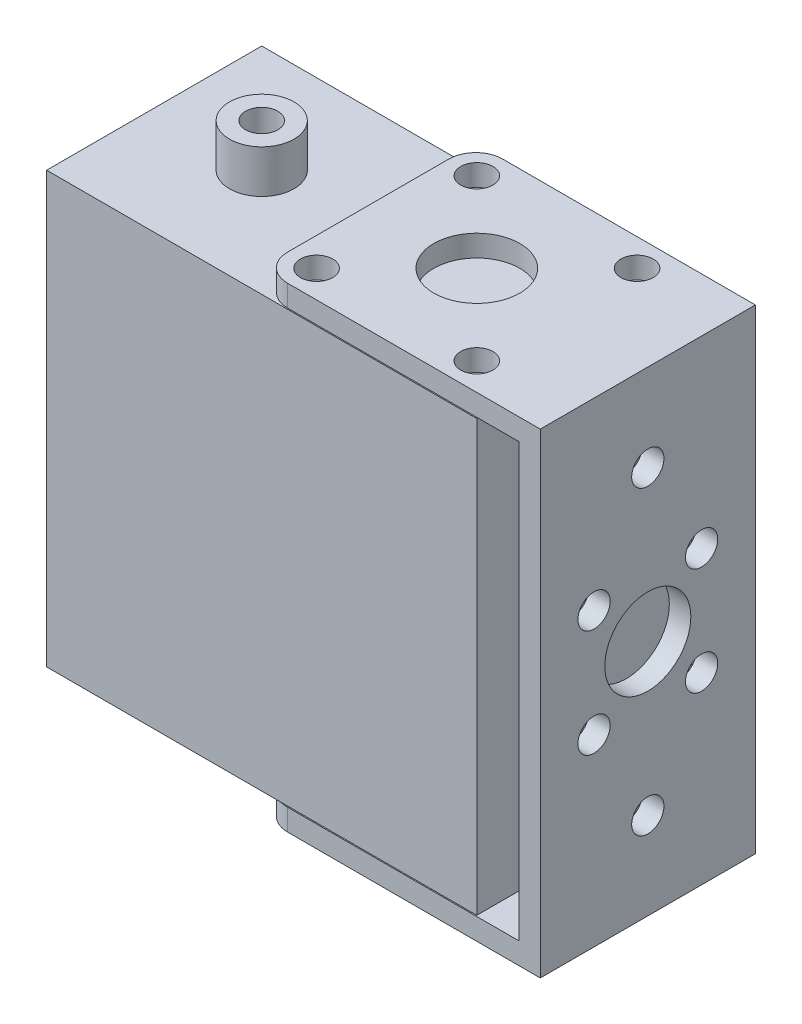
SolidWorks part; units mm, degrees
ref_plane "Alzado" through (0, 0, 0) normal (0, 0, 1) x (1, 0, 0)
ref_plane "Planta" through (0, 0, 0) normal (0, 1, 0) x (1, 0, 0)
ref_plane "Vista lateral" through (0, 0, 0) normal (1, 0, 0) x (0, 0, -1)
sketch "Croquis1" plane through (0, 0, 0) normal (0, 0, 1) x (1, 0, 0)
  line L0 (-13, -20.1) -> (11, -20.1)
  line L1 (-13, -22.1) -> (13, -22.1)
  line L2 (-13, -22.1) -> (-13, 22.1)
  line L3 (-13, 22.1) -> (13, 22.1)
  line L4 (13, -22.1) -> (13, 22.1)
  line L5 (-13, -22.1) -> (13, 22.1) construction
  line L6 (-13, 22.1) -> (13, -22.1) construction
  line L7 (-13, 20.1) -> (11, 20.1)
  line L8 (11, 20.1) -> (11, -20.1)
  point P0 (0, 0)
  dimension "D1" = 44.2
extrude "Saliente-Extruir1" add sketch "Croquis1" along normal blind 20 contours L7 L8 L0 L2 L1 L4 L3
sketch "Croquis2" plane through (0, 22.1, 0) normal (0, 1, 0) x (1, 0, 0)
  line L0 (-13, -20) -> (-13, 0)
  line L1 (-13, 0) -> (13, 0)
  line L2 (13, 0) -> (13, -20)
  line L3 (13, -20) -> (-13, -20)
  line L4 (-13, -17.5) -> (-13, -2.5)
  line L5 (-10.5, -20) -> (-13, -20)
  line L6 (-10.5, -20) -> (-2.5, -20)
  line L8 (-10.5, 0) -> (-2.5, 0)
  line L10 (-13, 0) -> (-10.5, 0)
  arc A1 (-10.5, 0) -> (-13, -2.5) centre (-10.5, -2.5) ccw
  arc A2 (-13, -17.5) -> (-10.5, -20) centre (-10.5, -17.5) ccw
  line M13 (13, 0) -> (-13, 0)
  line M14 (-13, 0) -> (-13, -20)
  line M15 (-13, -20) -> (13, -20)
extrude "Cortar-Extruir1" cut sketch "Croquis2" against normal through all contours A2 M14 M15 | A1 M13 M14
sketch "Croquis3" plane through (0, 22.1, 0) normal (0, 1, 0) x (1, 0, 0)
  circle A1 centre (-2.9, -10) radius 4
  circle A2 centre (-10.35, -17.45) radius 1.5
  circle A3 centre (-10.35, -2.55) radius 1.5
  circle A4 centre (4.55, -17.45) radius 1.5
  circle A5 centre (4.55, -2.55) radius 1.5
extrude "Cortar-Extruir2" cut sketch "Croquis3" against normal through all both and the other way through all
sketch "Croquis4" plane through (13, 0, 0) normal (1, 0, 0) x (0, 0, -1)
  line L9 (-15, -5) -> (-5, 5) construction
  line L10 (-15, 5) -> (-5, -5) construction
  circle A0 centre (-10, 0) radius 4
  circle A1 centre (-15, 5) radius 1.5
  circle A2 centre (-5, 5) radius 1.5
  circle A3 centre (-5, -5) radius 1.5
  circle A4 centre (-15, -5) radius 1.5
  point P22 (-10, 0)
extrude "Cortar-Extruir3" cut sketch "Croquis4" against normal blind 20
sketch "Croquis5" plane through (13, 0, 0) normal (1, 0, 0) x (0, 0, -1)
  circle A1 centre (-10, 14) radius 1.5
  circle A2 centre (-10, -14) radius 1.5
extrude "Cortar-Extruir4" cut sketch "Croquis5" against normal blind 20
ref_plane "Plano1" through (0, 0, 0) normal (0, 1, 0) x (1, 0, 0)
sketch "Croquis7" plane through (0, 0, 0) normal (0, 1, 0) x (1, 0, 0)
  line L0 (-2.9, -10) -> (-22.9, -10) construction
  circle A0 centre (-22.9, -10) radius 1
extrude "Saliente-Extruir2" add sketch "Croquis7" along normal mid plane 20 separate body
sketch "Croquis8" plane through (0, 0, 0) normal (0, 1, 0) x (1, 0, 0)
  line L1 (-32.9, 0) -> (-12.9, 0)
  line L2 (-32.9, 0) -> (-32.9, -20)
  line L3 (-32.9, -20) -> (-12.9, -20)
  line L4 (-12.9, 0) -> (-12.9, -20)
  line L5 (-32.9, 0) -> (-12.9, -20) construction
  line L6 (-32.9, -20) -> (-12.9, 0) construction
  line L7 (-12.9, 0) -> (7.1, 0)
  line L8 (-12.9, 0) -> (-12.9, -20)
  line L9 (-12.9, -20) -> (7.1, -20)
  line L10 (7.1, 0) -> (7.1, -20)
  circle A0 centre (-22.9, -10) radius 1.5
  point P0 (-22.9, -10)
extrude "Saliente-Extruir4" add sketch "Croquis8" along normal mid plane 40 separate body contours L4 L1 L2 L3 A0 | L10 L7 L4 L9
sketch "Croquis9" plane through (0, -20, 0) normal (0, -1, 0) x (-1, 0, 0)
  circle A0 centre (22.9, -10) radius 1.5
  circle A1 centre (22.9, -10) radius 3
extrude "Saliente-Extruir5" add sketch "Croquis9" along normal blind 4
mirror "Simetría1" about plane through (0, 0, 0) normal (0, 1, 0) of "Saliente-Extruir5"
